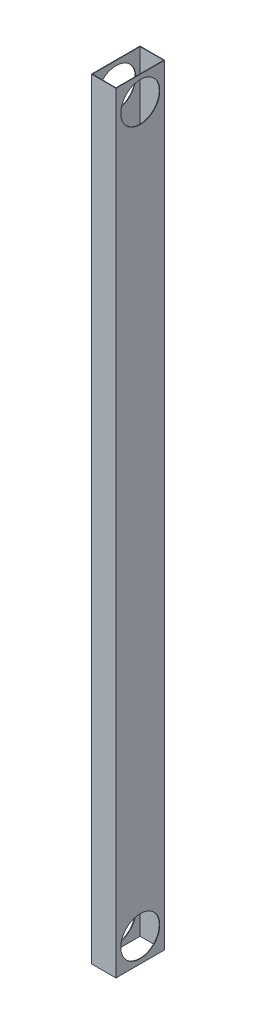
SolidWorks part; units mm, degrees
ref_plane "Front Plane" through (0, 0, 0) normal (0, 0, 1) x (1, 0, 0)
ref_plane "Top Plane" through (0, 0, 0) normal (0, 1, 0) x (1, 0, 0)
ref_plane "Right Plane" through (0, 0, 0) normal (1, 0, 0) x (0, 0, -1)
sketch "Sketch2" plane through (0, 0, 0) normal (0, 1, 0) x (1, 0, 0)
  line L0 (-24.5, 49.5) -> (24.5, 49.5)
  line L1 (-25.5, 50.5) -> (25.5, 50.5)
  line L2 (-25.5, 50.5) -> (-25.5, -50.5)
  line L3 (-25.5, -50.5) -> (25.5, -50.5)
  line L4 (25.5, 50.5) -> (25.5, -50.5)
  line L5 (24.5, 49.5) -> (24.5, -49.5)
  line L6 (-24.5, -49.5) -> (24.5, -49.5)
  line L7 (-24.5, 49.5) -> (-24.5, -49.5)
  point P4 (-25.5, 0)
  point P6 (0, 50.5)
  point P11 (0, 0)
  dimension "D1" = 101
  dimension "D2" = 51
  dimension "D3" = 1
extrude "Boss-Extrude2" add sketch "Sketch2" along normal blind 1600 contours L4 L1 L2 L3 L7 L0 L5 L6
sketch "Sketch3" plane through (-25.5, 0, 0) normal (-1, 0, 0) x (0, 0, 1)
  circle A0 centre (0, 50) radius 40.5
  circle A1 centre (0, 1550) radius 40.5
  point P2 (0, 0)
  dimension "D1" = 81
  dimension "D3" = 81
  dimension "D2" = 50
  dimension "D4" = 1500
extrude "Cut-Extrude2" cut sketch "Sketch3" against normal through all contours A0
